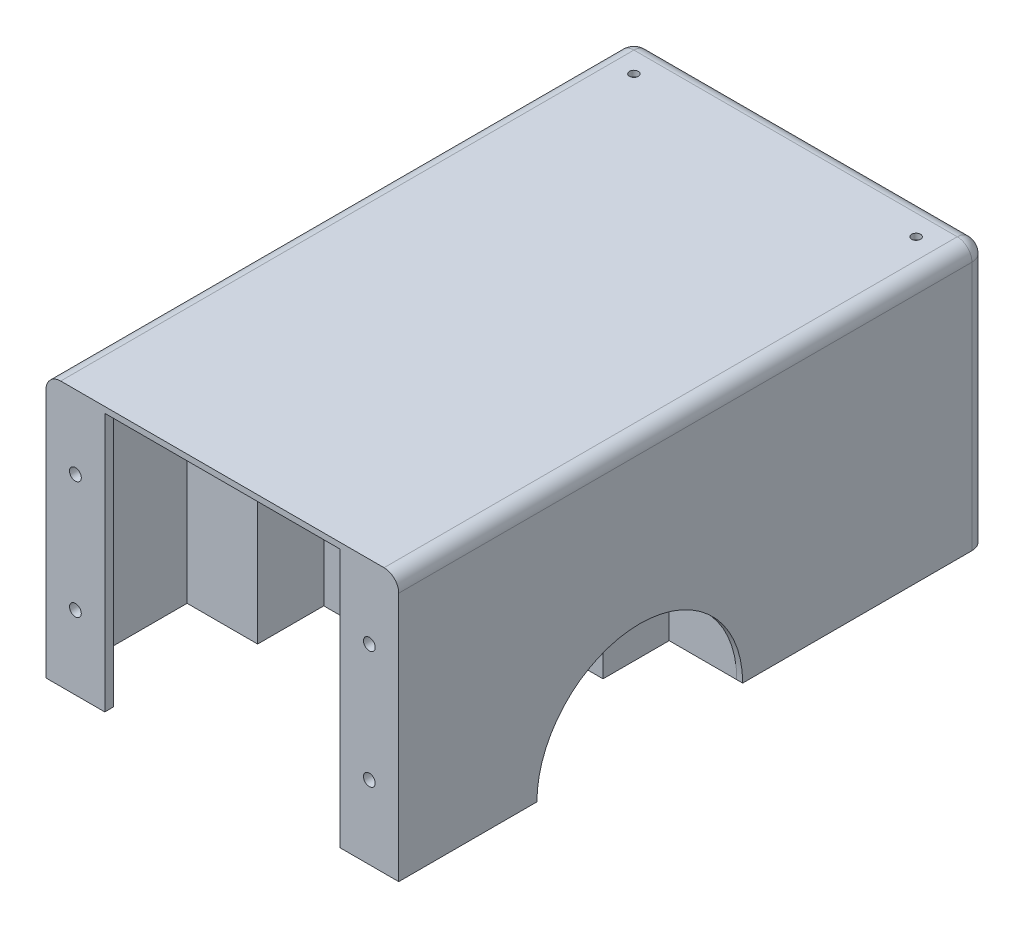
SolidWorks part; units mm, degrees
material "ABS"
ref_plane "Front Plane" through (0, 0, 0) normal (0, 0, 1) x (1, 0, 0)
ref_plane "Top Plane" through (0, 0, 0) normal (0, 1, 0) x (1, 0, 0)
ref_plane "Right Plane" through (0, 0, 0) normal (1, 0, 0) x (0, 0, -1)
sketch "Sketch1" plane through (0, 0, 0) normal (1, 0, 0) x (0, 0, -1)
  line L0 (35, 0) -> (118, 0)
  line L1 (118, 0) -> (118, 90)
  line L4 (118, 90) -> (-82, 90)
  line L5 (-82, 90) -> (-82, 0)
  line L6 (-82, 0) -> (-35, 0)
  arc A0 (-35, 0) -> (35, 0) centre (0, 0) cw
  dimension "D2" = 35
  dimension "D1" = 90
  dimension "D3" = 118
  dimension "D4" = 200
extrude "Boss-Extrude1" add sketch "Sketch1" along normal blind 60
fillet "Fillet1" radius 5 3 edges at (60, 90, -18) (30, 90, -118) (60, 45, -118)
shell "Shell1" thickness 2
sketch "Sketch2" plane through (0, 88, 0) normal (0, -1, 0) x (1, 0, 0)
  line L1 (0, -113) -> (0, 82) construction
  line L2 (55, -116) -> (0, -116) construction
  circle A0 centre (41, -76) radius 2.675
  circle A1 centre (41, -76) radius 1.425 construction
  dimension "D2" = 2.85
  dimension "D3" = 1.25
  dimension "D1" = 82
  dimension "D4" = 40
extrude "Boss-Extrude2" add sketch "Sketch2" along normal blind 27
sketch "Sketch3" plane through (0, 61, 0) normal (0, -1, 0) x (1, 0, 0)
  circle A0 centre (41, -76) radius 1.425
  dimension "D1" = 2.85
extrude "Cut-Extrude1" cut sketch "Sketch3" against normal blind 4
sketch "Sketch4" plane through (0, 0, 0) normal (0, -1, 0) x (1, 0, 0)
  line L0 (60, 82) -> (60, 35) construction
  line L1 (58, 82) -> (40, 82)
  line L2 (58, 82) -> (58, 79)
  line L3 (58, 79) -> (40, 79)
  line L4 (40, 82) -> (40, 79)
  dimension "D1" = 20
  dimension "D2" = 3
extrude "Boss-Extrude3" add sketch "Sketch4" against normal up to surface (88 mm away) up to face at (41, 88, -78.675)
sketch "Sketch5" plane through (0, 0, 82) normal (0, 0, 1) x (1, 0, 0)
  line L0 (40, 88) -> (40, 0) construction
  line L1 (55, 90) -> (0, 90) construction
  line L2 (60, 0) -> (40, 0) construction
  circle A0 centre (50, 25) radius 2
  circle A1 centre (50, 65) radius 2
  point P4 (0, 0)
  dimension "D4" = 4
  dimension "D1" = 10
  dimension "D2" = 25
  dimension "D3" = 25
extrude "Cut-Extrude2" cut sketch "Sketch5" against normal up to surface (3 mm away) up to face at (50.3243, 52.3243, 79)
sketch "Sketch6" plane through (0, 0, 0) normal (0, -1, 0) x (1, 0, 0)
  line L0 (58, 35) -> (35, 35)
  line L1 (35, 35) -> (35, 12.5)
  line L2 (35, 12.5) -> (15, 12.5)
  line L3 (15, 12.5) -> (15, -12.5)
  line L4 (15, -12.5) -> (35, -12.5)
  line L5 (35, -12.5) -> (35, -35)
  line L6 (35, -35) -> (58, -35)
  line L7 (58, -35) -> (58, -36)
  line L8 (58, -113) -> (58, 79) construction
  line L9 (58, -36) -> (34, -36)
  line L10 (34, -36) -> (34, -13.5)
  line L11 (34, -13.5) -> (14, -13.5)
  line L12 (14, -13.5) -> (14, 13.5)
  line L13 (14, 13.5) -> (34, 13.5)
  line L14 (34, 13.5) -> (34, 36)
  line L15 (34, 36) -> (58, 36)
  line L16 (58, 79) -> (58, 35) construction
  line L17 (58, 36) -> (58, 35)
  line L18 (60, -35) -> (60, 35) construction
  point P22 (38.0371, 41.3573)
  point P23 (43.8936, -5.037)
  point P24 (42.745, -14.6853)
  point P25 (23.4486, -20.1985)
  point P26 (36.082, -13.5139)
  dimension "D1" = 1
  dimension "D2" = 1
  dimension "D3" = 1
  dimension "D4" = 1
  dimension "D5" = 25
  dimension "D6" = 20
  dimension "D7" = 25
extrude "Boss-Extrude4" add sketch "Sketch6" against normal up to surface (88 mm away) up to face at (31.6667, 88, 16)
sketch "Sketch8" plane through (0, 90, 0) normal (0, 1, 0) x (1, 0, 0)
  line L0 (60, 113) -> (60, -82) construction
  line L1 (0, 118) -> (55, 118) construction
  circle A0 centre (48, 106) radius 1.5
  dimension "D1" = 3
  dimension "D2" = 12
  dimension "D3" = 12
extrude "Cut-Extrude3" cut sketch "Sketch8" against normal up to surface (2 mm away) up to face at (33.1429, 88, 6.8571)
sketch "Sketch9" plane through (0, 88, 0) normal (0, -1, 0) x (1, 0, 0)
  line L0 (46.5858, -105.5) -> (49.4142, -105.5)
  line L1 (49.4142, -106.5) -> (46.5858, -106.5)
  circle A0 centre (48, -106) radius 2.5
  arc A1 (46.5858, -105.5) -> (46.5858, -106.5) centre (48, -106) ccw
  arc A2 (49.4142, -106.5) -> (49.4142, -105.5) centre (48, -106) ccw
  circle A3 centre (48, -106) radius 1.5 construction
  dimension "D2" = 1
  dimension "D1" = 1
extrude "Boss-Extrude5" add sketch "Sketch9" along normal blind 1
sketch "Sketch10" plane through (14, 0, 0) normal (-1, 0, 0) x (0, 0, 1)
  line L0 (0, 0) -> (0, 75.1423) construction
  line L2 (36, 0) -> (13.5, 0) construction
  circle A0 centre (0, 0) radius 4
  circle A1 centre (-8.75, 20.5) radius 1.5
  circle A2 centre (8.75, 20.5) radius 1.5
  circle A3 centre (-8.75, 47) radius 2
  circle A4 centre (8.75, 47) radius 2
  point P11 (0, 0)
  point P12 (0, 0)
  point P15 (10.0249, 0)
  dimension "D1" = 8
  dimension "D2" = 3
  dimension "D6" = 4
  dimension "D3" = 17.5
  dimension "D4" = 20.5
  dimension "D5" = 26.5
  dimension "D7" = 17.5
extrude "Cut-Extrude4" cut sketch "Sketch10" against normal up to surface (1 mm away) up to face at (15, 44, 0)
mirror "Mirror1" about plane through (0, 0, 0) normal (1, 0, 0) of bodies 112 102
sketch "Sketch11" plane through (0, 88, 0) normal (0, -1, 0) x (1, 0, 0)
  line L0 (0, 0) -> (0, 72.8107) construction
  line L1 (-14, 13.5) -> (-34, 13.5) construction
  circle A0 centre (18.69, 23.5) radius 1.425
  circle A1 centre (18.69, 23.5) radius 2.425
  circle A2 centre (18.69, 60.24) radius 1.425
  circle A3 centre (18.69, 60.24) radius 2.425
  circle A4 centre (-18.69, 60.24) radius 1.425
  circle A5 centre (-18.69, 60.24) radius 2.425
  circle A6 centre (-18.69, 23.5) radius 1.425
  circle A7 centre (-18.69, 23.5) radius 2.425
  dimension "D1" = 1
  dimension "D2" = 2.85
  dimension "D3" = 36.74
  dimension "D4" = 37.38
  dimension "D5" = 10
extrude "Boss-Extrude6" add sketch "Sketch11" along normal blind 3
